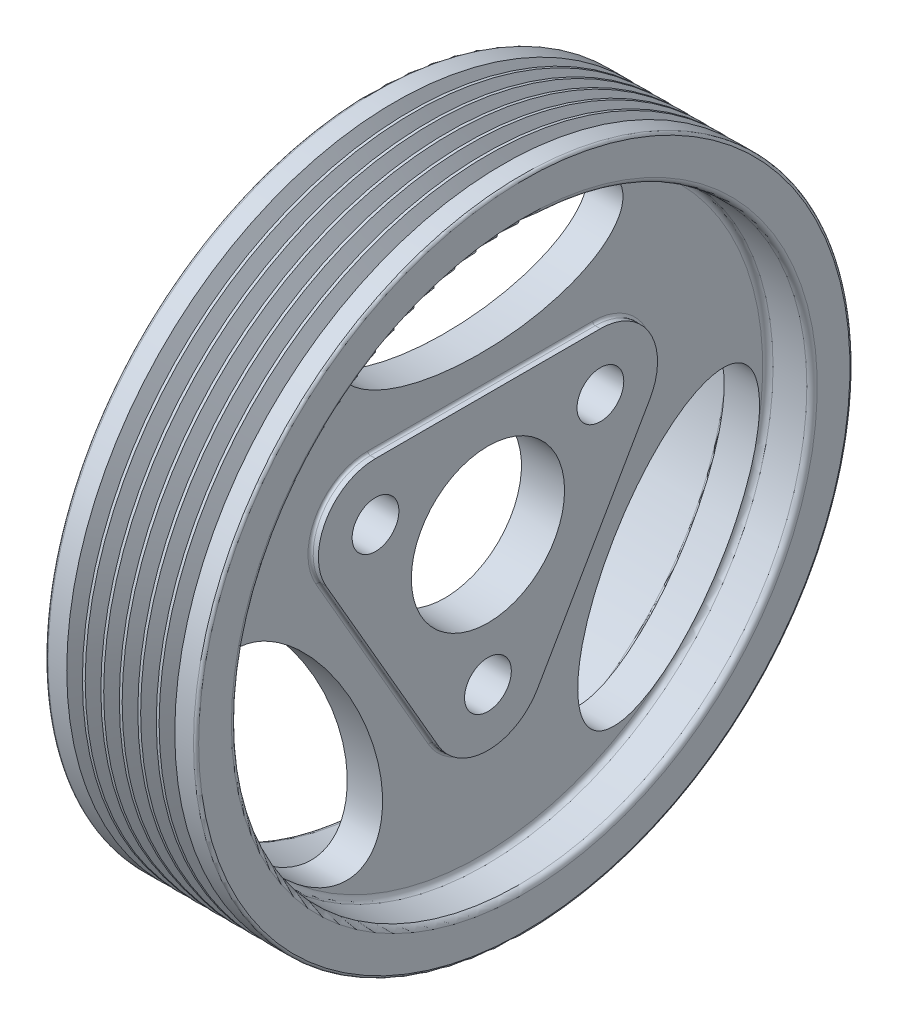
SolidWorks part; units mm, degrees
material "AISI 1010 Сталь, горяченакатанная полоса"
ref_plane "Спереди" through (0, 0, 0) normal (0, 0, 1) x (1, 0, 0)
ref_plane "Сверху" through (0, 0, 0) normal (0, 1, 0) x (1, 0, 0)
ref_plane "Справа" through (0, 0, 0) normal (1, 0, 0) x (0, 0, -1)
sketch "Эскиз1" plane through (0, 0, 0) normal (0, 0, 1) x (1, 0, 0)
  line L0 (13.7, 14.75) -> (20.5, 14.75)
  line L1 (20.5, 14.75) -> (20.5, 55.4)
  line L2 (20.5, 55.4) -> (29, 55.4)
  line L3 (29, 55.4) -> (29, 63.2)
  line L4 (29, 63.2) -> (0, 63.2)
  line L5 (0, 63.2) -> (0, 55.4)
  line L6 (0, 55.4) -> (13.7, 55.4)
  line L7 (13.7, 55.4) -> (13.7, 14.75)
  line L8 (-584.1514, 0) -> (28623.4206, 0) construction
  dimension "D1" = 29
  dimension "D2" = 126.4
  dimension "D3" = 29.5
  dimension "D4" = 7.8
  dimension "D5" = 8.5
  dimension "D6" = 13.7
revolve "Повернуть1" add sketch "Эскиз1" angle 360 about L8
fillet "Скругление1" radius 1 4 edges at (0, 0, 55.4) (13.7, 0, 55.4) (20.5, 0, 55.4) (29, 0, 55.4)
fillet "Скругление2" radius 0.5 2 edges at (29, 0, 63.2) (0, 0, 63.2)
sketch "Эскиз2" plane through (0, 0, 0) normal (0, 1, 0) x (1, 0, 0)
  line L0 (3.8285, 63.7) -> (5.6071, 60.4243)
  line L1 (5.6071, 60.4243) -> (7.3857, 63.7)
  line L2 (7.3857, 63.7) -> (9.1643, 60.4243)
  line L3 (9.1643, 60.4243) -> (10.9428, 63.7)
  line L4 (10.9428, 63.7) -> (12.7214, 60.4243)
  line L5 (12.7214, 60.4243) -> (14.5, 63.7)
  line L6 (14.5, 63.7) -> (16.2786, 60.4243)
  line L7 (16.2786, 60.4243) -> (18.0572, 63.7)
  line L8 (18.0572, 63.7) -> (19.8357, 60.4243)
  line L9 (19.8357, 60.4243) -> (21.6143, 63.7)
  line L10 (21.6143, 63.7) -> (23.3929, 60.4243)
  line L11 (23.3929, 60.4243) -> (25.1715, 63.7)
  line L12 (3.8285, 63.7) -> (3.8285, 68.7)
  line L13 (3.8285, 68.7) -> (25.1715, 68.7)
  line L14 (25.1715, 68.7) -> (25.1715, 63.7)
  line L15 (3.8285, 63.7) -> (25.1715, 63.7) construction
  line L18 (28.5, 63.2) -> (0.5, 63.2) construction
  line L19 (28.5, 63.2) -> (0.5, 63.2) construction
  line L21 (28.5, 63.2) -> (0.5, 63.2) construction
  line L22 (0, 62.7) -> (0, -62.7) construction
  line L23 (29, -62.7) -> (29, 62.7) construction
  point P21 (24.9, 63.2)
  point P22 (4.1, 63.2)
  dimension "D1" = 5
  dimension "D4" = 57
  dimension "D5" = 0.5
  dimension "D3" = 4.1
  dimension "D6" = 3.5572
  dimension "D2" = 4.1
  dimension "D7" = 21.343
revolve "Повернуть2" add sketch "Эскиз2" angle 360 about L8
combine bodies "Соединить1" operation type subtract main body 103 bodies to subtract 104
sketch "Эскиз3" plane through (13.7, 0, 0) normal (-1, 0, 0) x (0, 0, 1)
  line L0 (0, -1000) -> (0, 49000) construction
  circle A0 centre (0, 0) radius 54.4 construction
  circle A1 centre (0, -25) radius 4.5
  circle A2 centre (-21.6506, 12.5) radius 4.5
  circle A3 centre (21.6506, 12.5) radius 4.5
  ellipse E0 centre (0, 41.9) end of major axis (27.5, 41.9) minor radius 12.5
  ellipse E1 centre (36.2865, -20.95) end of major axis (22.5365, -44.7657) minor radius 12.5
  ellipse E2 centre (-36.2865, -20.95) end of major axis (-50.0365, 2.8657) minor radius 12.5
  point P32 (0, 0)
  dimension "D4" = 9
  dimension "D1" = 55
  dimension "D2" = 25
  dimension "D3" = 25
  dimension "D5" = 3
extrude "Вырез-Вытянуть1" cut sketch "Эскиз3" against normal through all both and the other way through all
sketch "Эскиз4" plane through (20.5, 0, 0) normal (1, 0, 0) x (0, 0, -1)
  line L0 (-21.6506, 23.5) -> (21.6506, 23.5)
  line L1 (31.1769, 7) -> (9.5263, -30.5)
  line L2 (-31.1769, 7) -> (-9.5263, -30.5)
  arc A1 (31.1769, 7) -> (21.6506, 23.5) centre (21.6506, 12.5) ccw
  arc A2 (-9.5263, -30.5) -> (9.5263, -30.5) centre (0, -25) ccw
  arc A3 (-21.6506, 23.5) -> (-31.1769, 7) centre (-21.6506, 12.5) ccw
  circle A4 centre (21.6506, 12.5) radius 4.5 construction
  circle A5 centre (0, -25) radius 4.5 construction
  circle A6 centre (-21.6506, 12.5) radius 4.5 construction
  circle A7 centre (0, 0) radius 14.75 construction
  circle A8 centre (21.6506, 12.5) radius 4.5
  circle A9 centre (0, -25) radius 4.5
  circle A10 centre (-21.6506, 12.5) radius 4.5
  circle A11 centre (0, 0) radius 14.75
  dimension "D1" = 6.5
extrude "Бобышка-Вытянуть1" add sketch "Эскиз4" along normal blind 1.5
fillet "Скругление3" radius 0.5 6 edges at (20.5, 18, -31.1769) (20.5, -11.75, -20.3516) (20.5, -36, 0) (20.5, -11.75, 20.3516) (20.5, 18, 31.1769) (20.5, 23.5, 0)
sketch "Эскиз5" plane through (13.7, 0, 0) normal (-1, 0, 0) x (0, 0, 1)
  circle A0 centre (-21.6506, 12.5) radius 8
  circle A1 centre (21.6506, 12.5) radius 8
  circle A2 centre (0, -25) radius 8
  circle A3 centre (0, -25) radius 4.5 construction
  dimension "D1" = 16
extrude "Вырез-Вытянуть2" cut sketch "Эскиз5" against normal blind 1
ref_plane "Плоскость1" through (4.1, 0, 0) normal (1, 0, 0) x (0, 0, -1)
ref_plane "Плоскость2" through (24.9, 0, 0) normal (1, 0, 0) x (0, 0, -1)
ref_plane "Середина шкива" through (14.5, 0, 0) normal (1, 0, 0) x (0, 0, -1)
equation "\"D2@Эскиз2\"=\"D3@Эскиз2\""
